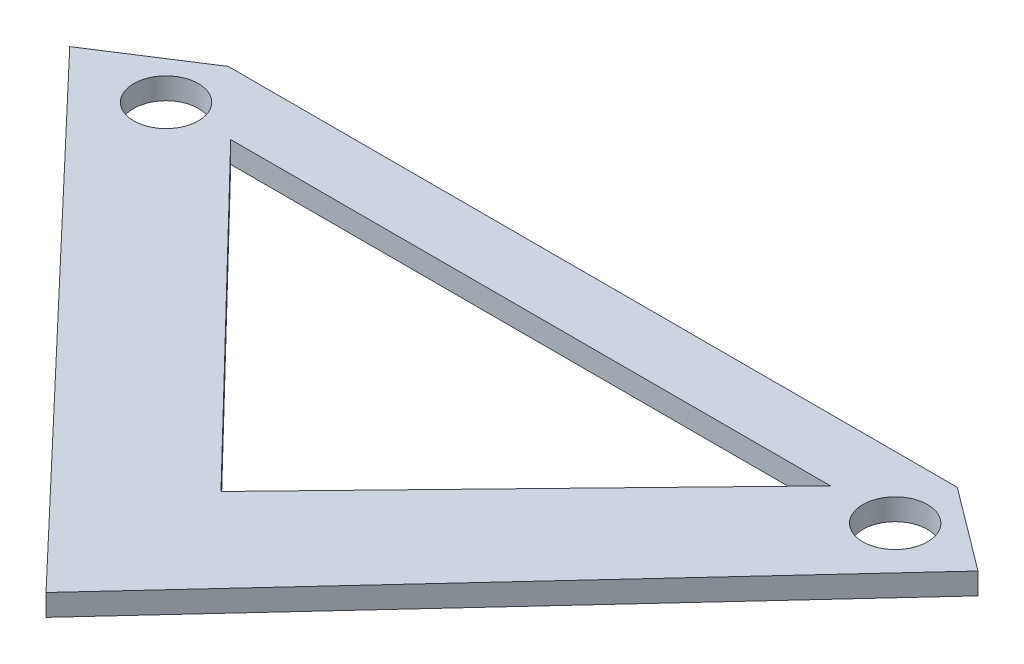
SolidWorks part; units mm, degrees
ref_plane "前视基准面" through (0, 0, 0) normal (0, 0, 1) x (1, 0, 0)
ref_plane "上视基准面" through (0, 0, 0) normal (0, 1, 0) x (1, 0, 0)
ref_plane "右视基准面" through (0, 0, 0) normal (1, 0, 0) x (0, 0, -1)
sketch "草图1" plane through (0, 0, 0) normal (0, 1, 0) x (1, 0, 0)
  line L0 (-14.4353, 0) -> (0, 0)
  line L1 (0, 0) -> (13.3937, 0)
  line L2 (13.3937, 0) -> (-0.5208, -14.3662)
  line L3 (-0.5208, -14.3662) -> (-14.4353, 0)
  line L4 (-17.4353, 2.8814) -> (16.3937, 2.8814)
  line L5 (16.3937, 2.8814) -> (20.2358, 0)
  line L6 (20.2358, 0) -> (-0.5208, -22.4849)
  line L7 (-17.4353, 2.8814) -> (-21.9037, 0)
  line L8 (-21.9037, 0) -> (-0.5208, -22.4849)
  circle A0 centre (-17.4353, 0) radius 1.5
  circle A1 centre (16.3937, 0) radius 1.5
  dimension "D4" = 3
  dimension "D5" = 3
  dimension "D1" = 20
  dimension "D2" = 20
  dimension "D3" = 3
  dimension "D6" = 3
extrude "凸台-拉伸4" add sketch "草图1" along normal blind 1
